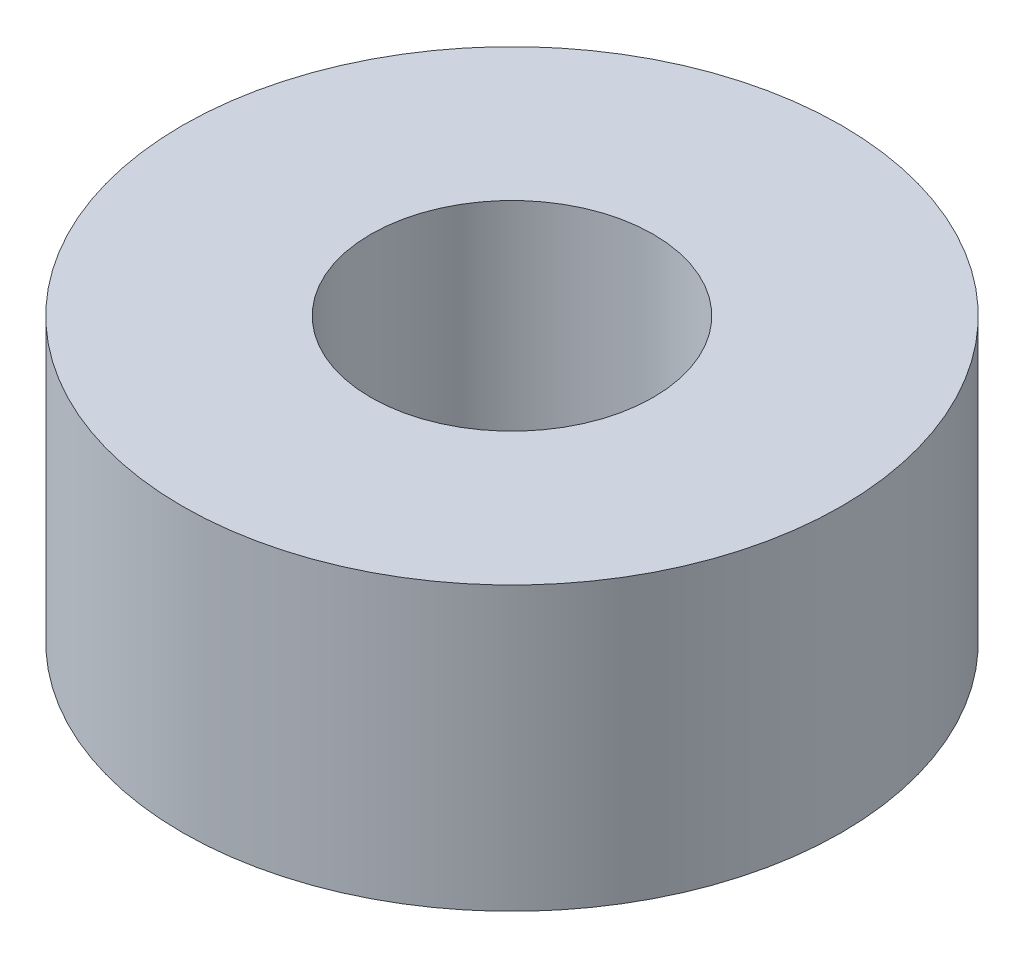
SolidWorks part; units mm, degrees
ref_plane "Front Plane" through (0, 0, 0) normal (0, 0, 1) x (1, 0, 0)
ref_plane "Top Plane" through (0, 0, 0) normal (0, 1, 0) x (1, 0, 0)
ref_plane "Right Plane" through (0, 0, 0) normal (1, 0, 0) x (0, 0, -1)
sketch "Sketch1" plane through (0, 0, 0) normal (0, 1, 0) x (1, 0, 0)
  circle A0 centre (0, 0) radius 1.5
  circle A1 centre (0, 0) radius 3.5
  dimension "D1" = 3
  dimension "D2" = 7
extrude "Boss-Extrude1" add sketch "Sketch1" along normal blind 3
